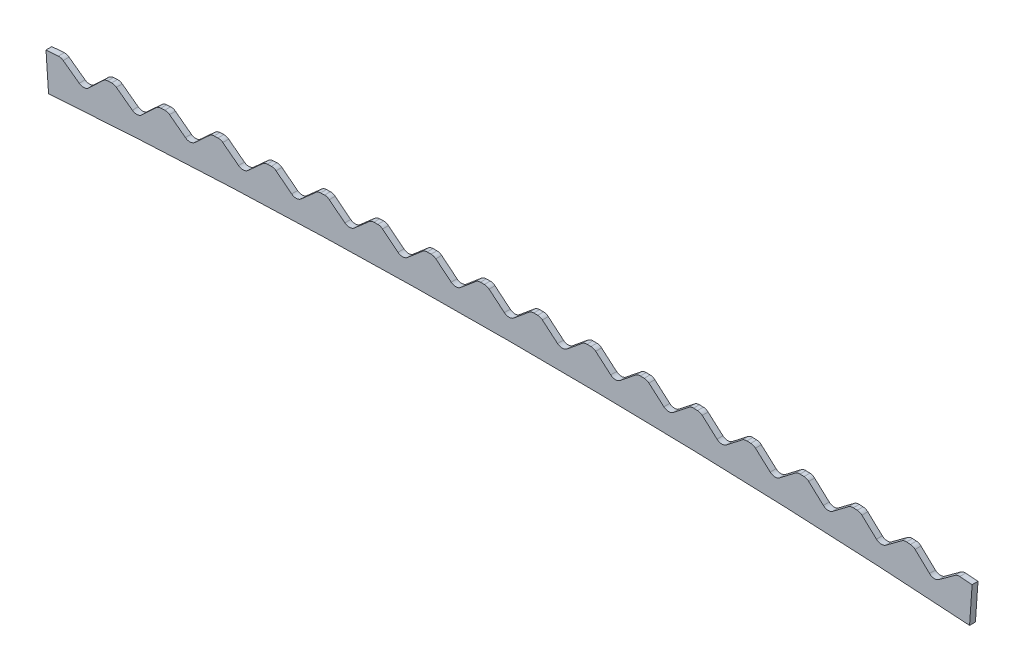
SolidWorks part; units mm, degrees
ref_plane "Plan de face" through (0, 0, 0) normal (0, 0, 1) x (1, 0, 0)
ref_plane "Plan de dessus" through (0, 0, 0) normal (0, 1, 0) x (1, 0, 0)
ref_plane "Plan de droite" through (0, 0, 0) normal (1, 0, 0) x (0, 0, -1)
sketch "Esquisse1" plane through (0, 0, 0) normal (0, 0, 1) x (1, 0, 0)
  line L0 (0, 0) -> (0, 2581.6249) construction
  line L1 (0, -9000) -> (-765.9347, 1953.3759) construction
  line L2 (0, -9000) -> (909.3505, 4004.3178) construction
  line L3 (627.8083, -21.9235) -> (631.2961, 27.9547)
  line L4 (-627.8083, -21.9235) -> (-631.2961, 27.9547)
  arc A0 (-627.8083, -21.9235) -> (627.8083, -21.9235) centre (0, -9000) cw
  arc A1 (-631.2961, 27.9547) -> (631.2961, 27.9547) centre (0, -9000) cw
  point P3 (0, 0)
  point P8 (0, 50)
  point P46 (0, -16000)
  point P60 (-0.6877, -10183.3172)
  point P110 (0, -10000)
  dimension "D1" = 9000
  dimension "D3" = 50
  dimension "D2" = 8
extrude "Boss.-Extru.2" add sketch "Esquisse1" along normal blind 8
sketch "Esquisse2" plane through (0, 0, 8) normal (0, 0, 1) x (1, 0, 0)
  line L0 (0, 25) -> (30, 49.9503)
  line L2 (30, 49.9503) -> (0, 74.9953)
  line L3 (0, 74.9953) -> (-30, 49.9503)
  line L4 (-30, 49.9503) -> (0, 25)
  line L5 (0, 0) -> (0, 50) construction
  arc A1 (631.2961, 27.9547) -> (-631.2961, 27.9547) centre (0, -9000) ccw construction
  arc A2 (631.2961, 27.9547) -> (-631.2961, 27.9547) centre (0, -9000) ccw construction
  point P5 (0, 50)
  dimension "D1" = 25
  dimension "D2" = 30
  dimension "D3" = 49.9953
extrude "Enlèv. mat.-Extru.1" cut sketch "Esquisse2" against normal through all
fillet "Congé1" radius 10 3 edges at (30, 49.9503, 4) (-30, 49.9503, 4) (0, 25, 4)
pattern_circular "Répétition circulaire1" count 9 every 0.46 about axis through (0, -9000, 0) along (0, 0, 1) of "Congé1", "Enlèv. mat.-Extru.1"
pattern_circular "Répétition circulaire2" count 9 every 0.46 about axis through (0, -9000, 0) along (0, 0, 1) of "Congé1", "Enlèv. mat.-Extru.1"
